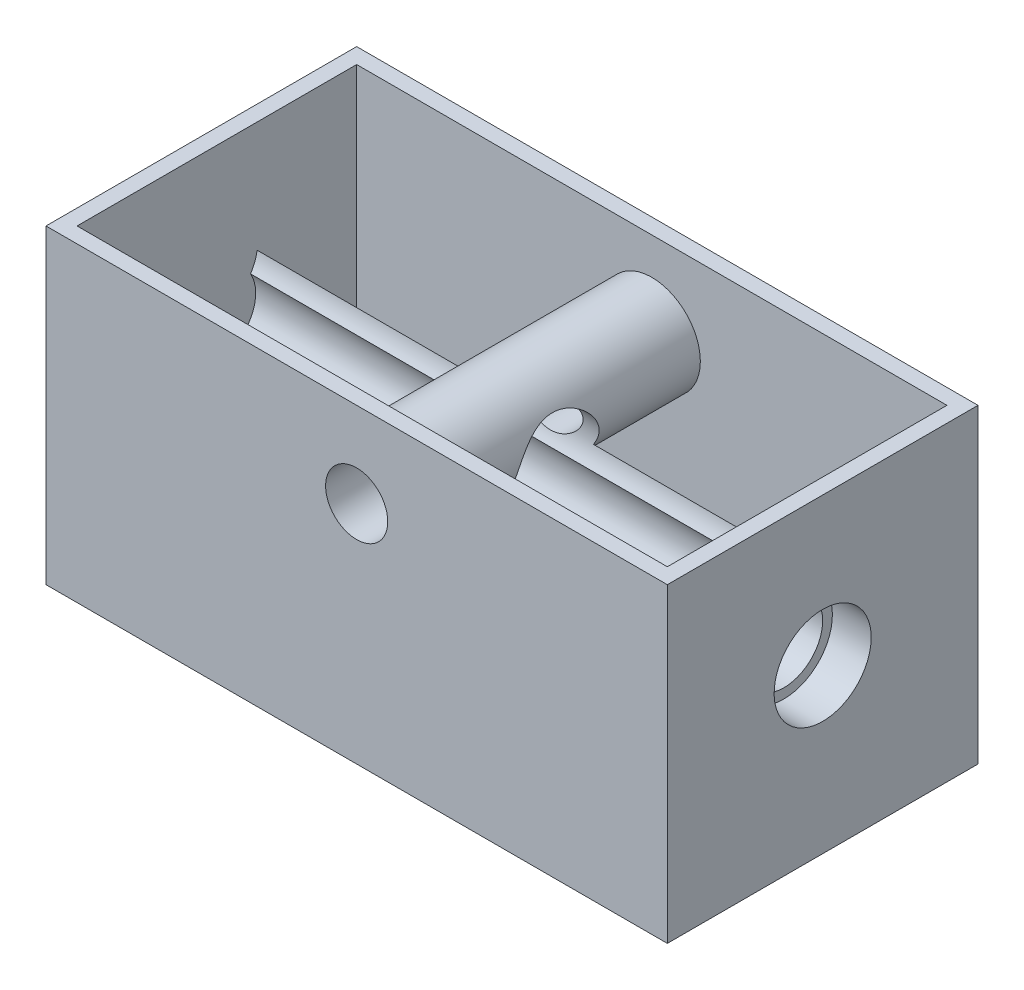
SolidWorks part; units mm, degrees
material "ASTM A36 Steel"
ref_plane "Front Plane" through (0, 0, 0) normal (0, 0, 1) x (1, 0, 0)
ref_plane "Top Plane" through (0, 0, 0) normal (0, 1, 0) x (1, 0, 0)
ref_plane "Right Plane" through (0, 0, 0) normal (1, 0, 0) x (0, 0, -1)
sketch "Sketch1" plane through (0, 0, 0) normal (0, 0, 1) x (1, 0, 0)
  line L1 (-50.8, 25.4) -> (50.8, 25.4)
  line L2 (-50.8, 25.4) -> (-50.8, -25.4)
  line L3 (-50.8, -25.4) -> (50.8, -25.4)
  line L4 (50.8, 25.4) -> (50.8, -25.4)
  line L5 (-50.8, 25.4) -> (50.8, -25.4) construction
  line L6 (-50.8, -25.4) -> (50.8, 25.4) construction
  point P0 (0, 0)
  dimension "D1" = 101.6
  dimension "D2" = 50.8
extrude "Boss-Extrude1" add sketch "Sketch1" against normal blind 50.8
sketch "Sketch2" plane through (50.8, 0, 0) normal (1, 0, 0) x (0, 0, -1)
  line L0 (50.8, 25.4) -> (0, 25.4) construction
  circle A0 centre (25.4, 1.27) radius 7.9375
  dimension "D1" = 15.875
  dimension "D2" = 24.13
extrude "Cut-Extrude1" cut sketch "Sketch2" against normal blind 6.35
sketch "Sketch3" plane through (50.8, 0, 0) normal (1, 0, 0) x (0, 0, -1)
  line L1 (50.8, 25.4) -> (0, 25.4) construction
  circle A0 centre (25.4, 1.27) radius 6.35
  dimension "D1" = 12.7
  dimension "D2" = 24.13
extrude "Cut-Extrude2" cut sketch "Sketch3" against normal through all
sketch "Sketch4" plane through (0, 0, -50.8) normal (0, 0, -1) x (-1, 0, 0)
  circle A1 centre (0, 11.4619) radius 5.3975
  dimension "D1" = 10.795
extrude "Cut-Extrude3" cut sketch "Sketch4" against normal blind 34.29
shell "Shell9" thickness 2.54
sketch "Sketch5" plane through (48.26, 0, 0) normal (-1, 0, 0) x (0, 0, 1)
  circle A3 centre (-25.037, 8.2826) radius 7.022
extrude "Cut-Extrude4" cut sketch "Sketch5" along normal up to surface (96.52 mm away) up to face at (-48.26, -7.62, -25.4)
sketch "Sketch6" plane through (0, 0, -13.97) normal (0, 0, 1) x (1, 0, 0)
  circle A0 centre (0, 11.4619) radius 5.3975
  dimension "D1" = 10.795
sketch "Sketch7" plane through (0, 0, -13.97) normal (0, 0, 1) x (1, 0, 0)
  circle A0 centre (0, 11.4619) radius 7.9375
  dimension "D1" = 15.875
extrude "Boss-Extrude3" add sketch "Sketch7" along normal up to surface (11.43 mm away) up to face at (0, 1.27, -2.54)
sketch "Sketch9" plane through (0, 0, 0) normal (0, 0, 1) x (1, 0, 0)
  circle A1 centre (0, 11.4619) radius 5.08
  dimension "D1" = 10.16
extrude "Cut-Extrude5" cut sketch "Sketch9" against normal blind 34.29
sketch "Sketch10" plane through (-50.8, 0, 0) normal (-1, 0, 0) x (0, 0, 1)
  circle A0 centre (-25.4, 1.27) radius 6.35
extrude "Boss-Extrude4" add sketch "Sketch10" against normal up to surface (2.54 mm away) up to face at (-48.26, 2.7246, -25.3247)
sketch "Sketch11" plane through (-50.8, 0, 0) normal (-1, 0, 0) x (0, 0, 1)
  circle A0 centre (-25.4, 1.27) radius 6.35 construction
  dimension "D1" = 12.7
sketch "Sketch12" plane through (50.8, 0, 0) normal (1, 0, 0) x (0, 0, -1)
  line L0 (50.8, 16.8594) -> (16.51, 16.8594) construction
  circle A0 centre (25.4, 11.4619) radius 5.3975 construction
  dimension "D1" = 10.795
sketch "Sketch13" plane through (0, 25.4, 0) normal (0, 1, 0) x (1, 0, 0)
  line L0 (-46.5734, 50.8) -> (-46.5734, 48.26)
  line L1 (50.8, 50.8) -> (-50.8, 50.8) construction
  line L2 (48.26, 48.26) -> (-48.26, 48.26) construction
